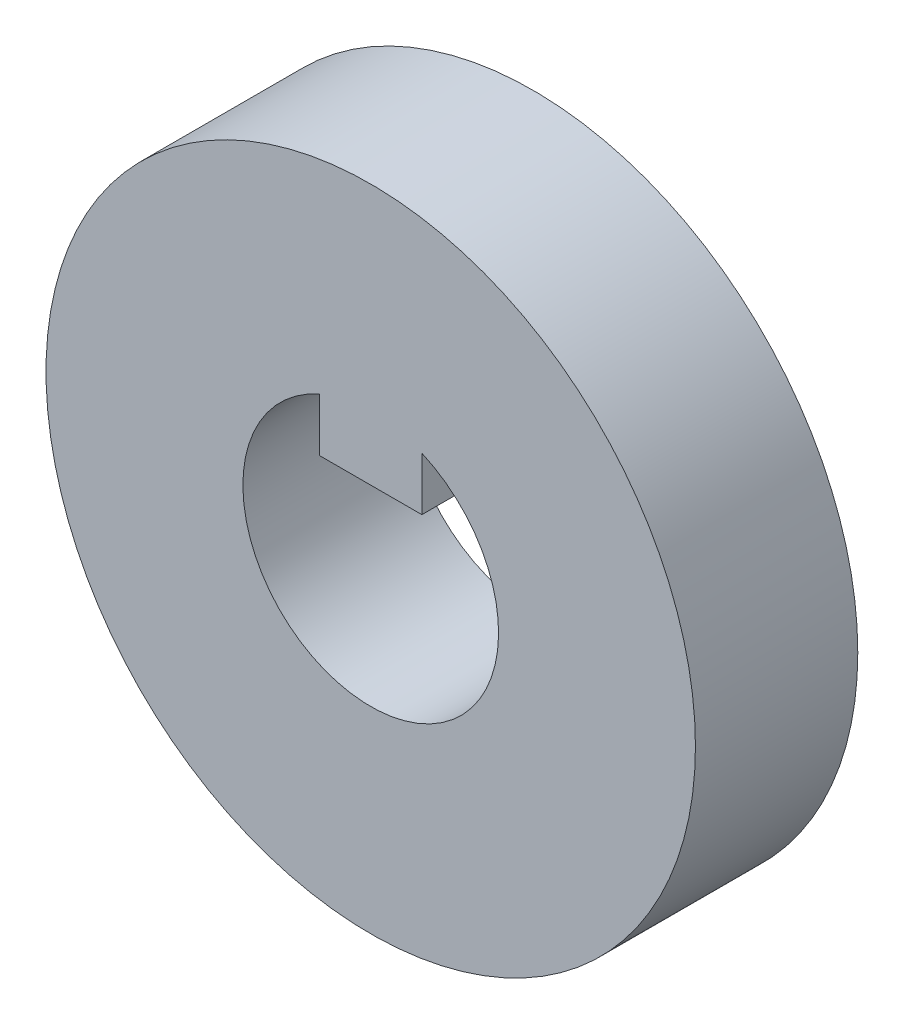
SolidWorks part; units mm, degrees
ref_plane "Front Plane" through (0, 0, 0) normal (0, 0, 1) x (1, 0, 0)
ref_plane "Top Plane" through (0, 0, 0) normal (0, 1, 0) x (1, 0, 0)
ref_plane "Right Plane" through (0, 0, 0) normal (1, 0, 0) x (0, 0, -1)
sketch "Sketch1" plane through (0, 0, 0) normal (0, 0, 1) x (1, 0, 0)
  line L1 (4, 15) -> (-4, 15)
  line L2 (4, 15) -> (4, 5)
  line L3 (4, 5) -> (-4, 5)
  line L4 (-4, 15) -> (-4, 5)
  line L5 (4, 15) -> (-4, 5) construction
  line L6 (4, 5) -> (-4, 15) construction
  circle A0 centre (0, 0) radius 25.4
  circle A1 centre (0, 0) radius 10
  point P4 (0, 10)
  dimension "D1" = 50.8
  dimension "D2" = 20
  dimension "D3" = 8
  dimension "D4" = 10
extrude "Boss-Extrude1" add sketch "Sketch1" along normal blind 12.7 contours A0 A1 L4 L1 L2
equation "\"shaftDiam\" = 20mm"
equation "\"keyW\" = 8mm"
equation "\"keyL\" = 10mm"
equation "\"clearance\" = 1mm"
equation "\"shafDiam_\"= \"shaftDiam\""
equation "\"keyL_\"= \"keyL\""
equation "\"keyW_\"= \"keyW\""
equation "\"D3@Sketch1\"=\"keyW_\""
equation "\"D4@Sketch1\"=\"keyL_\""
equation "\"D2@Sketch1\"=\"shafDiam_\""
